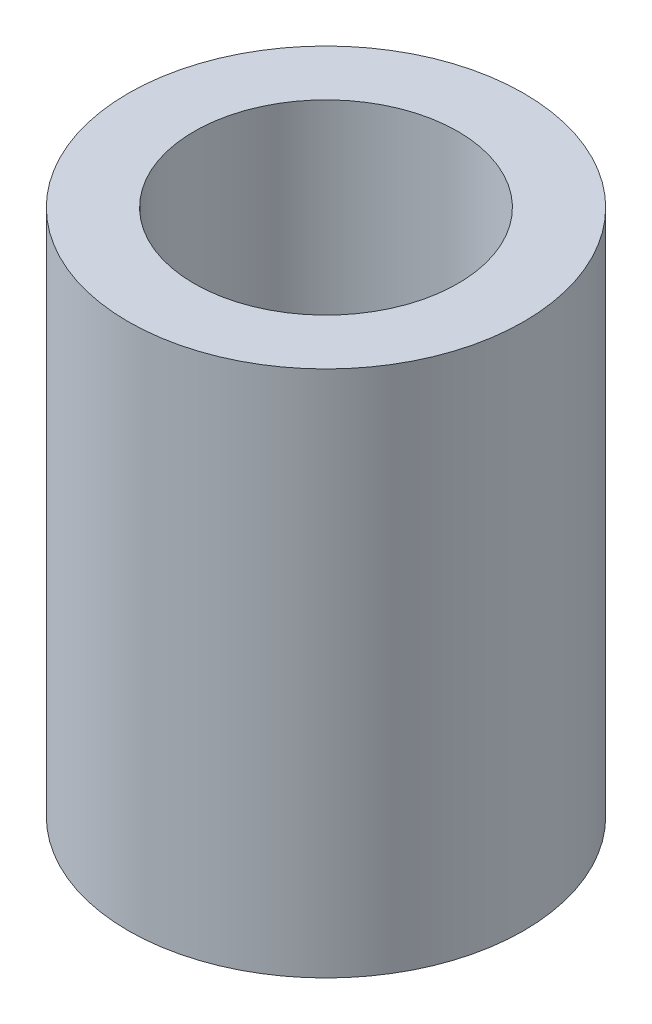
SolidWorks part; units mm, degrees
material "Commercial Bronze, UNS C22000 (90-10 Bronze)"
ref_plane "Front Plane" through (0, 0, 0) normal (0, 0, 1) x (1, 0, 0)
ref_plane "Top Plane" through (0, 0, 0) normal (0, 1, 0) x (1, 0, 0)
ref_plane "Right Plane" through (0, 0, 0) normal (1, 0, 0) x (0, 0, -1)
sketch "Sketch1" plane through (0, 0, 0) normal (0, 1, 0) x (1, 0, 0)
  circle A0 centre (0, 0) radius 2.25
  circle A1 centre (0, 0) radius 1.5
  dimension "D1" = 3
  dimension "D2" = 4.5
extrude "Boss-Extrude1" add sketch "Sketch1" along normal blind 6
